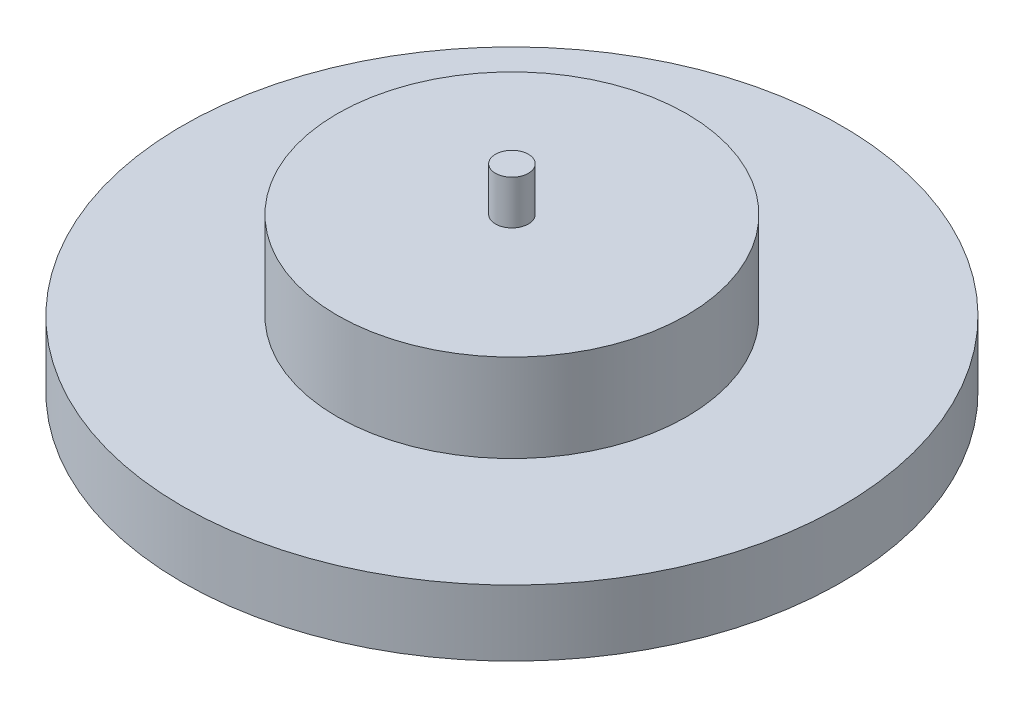
SolidWorks part; units mm, degrees
ref_plane "前视基准面" through (0, 0, 0) normal (0, 0, 1) x (1, 0, 0)
ref_plane "上视基准面" through (0, 0, 0) normal (0, 1, 0) x (1, 0, 0)
ref_plane "右视基准面" through (0, 0, 0) normal (1, 0, 0) x (0, 0, -1)
other "Configuration Table"
sketch "草图1" plane through (0, 0, 0) normal (0, 1, 0) x (1, 0, 0)
  circle A0 centre (0, 0) radius 15
  dimension "D1" = 30
extrude "凸台-拉伸1" add sketch "草图1" along normal blind 3
sketch "草图2" plane through (0, 3, 0) normal (0, 1, 0) x (1, 0, 0)
  circle A0 centre (0, 0) radius 7.95
  dimension "D1" = 15.9
extrude "凸台-拉伸2" add sketch "草图2" along normal blind 4
sketch "草图3" plane through (0, 7, 0) normal (0, 1, 0) x (1, 0, 0)
  circle A0 centre (0, 0) radius 0.75
  dimension "D1" = 1.5
extrude "凸台-拉伸3" add sketch "草图3" along normal blind 2
